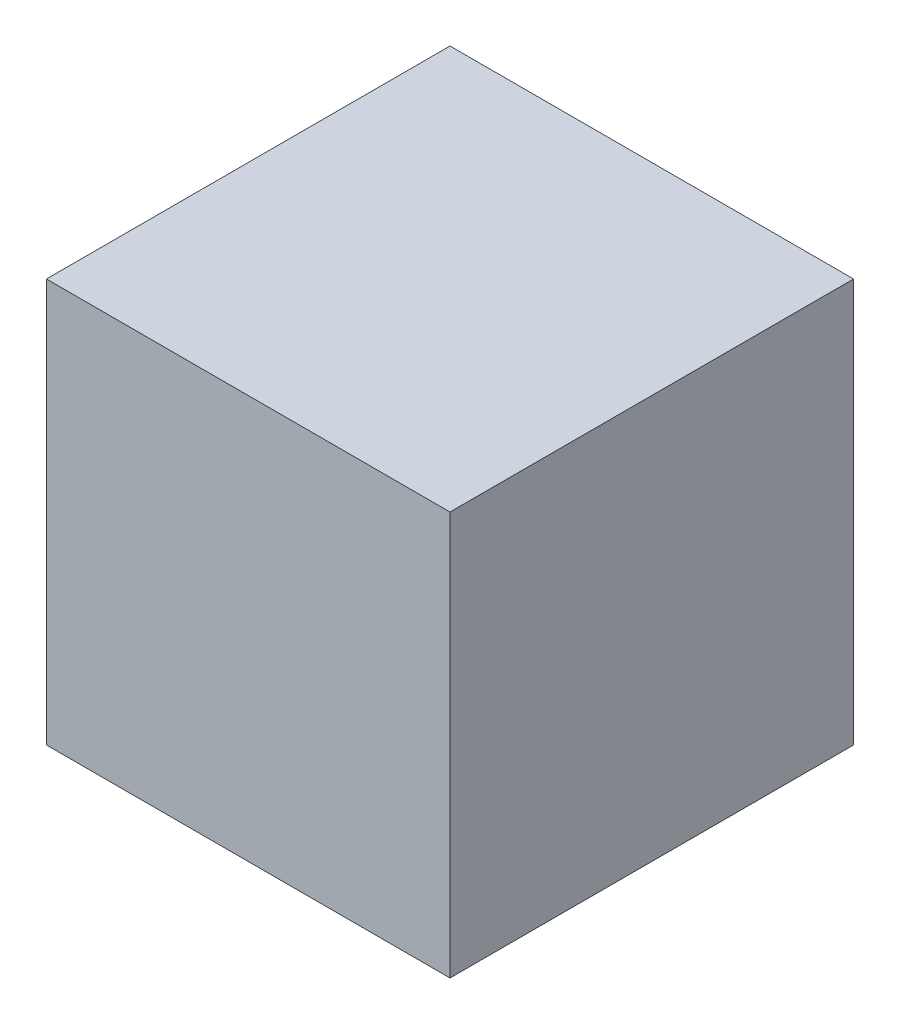
SolidWorks part; units mm, degrees
material "6061-T6 (SS)"
ref_plane "Front Plane" through (0, 0, 0) normal (0, 0, 1) x (1, 0, 0)
ref_plane "Top Plane" through (0, 0, 0) normal (0, 1, 0) x (1, 0, 0)
ref_plane "Right Plane" through (0, 0, 0) normal (1, 0, 0) x (0, 0, -1)
sketch "Sketch1" plane through (0, 0, 0) normal (0, 1, 0) x (1, 0, 0)
  line L1 (12.7, 12.7) -> (-12.7, 12.7)
  line L2 (12.7, 12.7) -> (12.7, -12.7)
  line L3 (12.7, -12.7) -> (-12.7, -12.7)
  line L4 (-12.7, 12.7) -> (-12.7, -12.7)
  line L5 (12.7, 12.7) -> (-12.7, -12.7) construction
  line L6 (12.7, -12.7) -> (-12.7, 12.7) construction
  point P0 (0, 0)
  dimension "D1" = 25.4
  dimension "D2" = 25.4
extrude "Boss-Extrude1" add sketch "Sketch1" along normal blind 25.4
